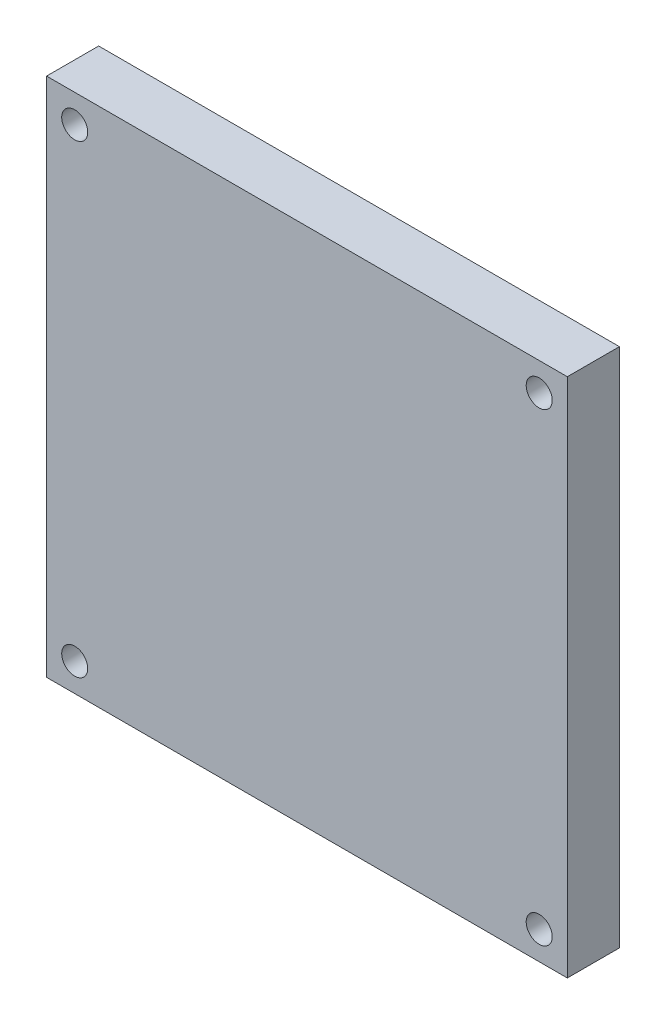
SolidWorks part; units mm, degrees
ref_plane "Front Plane" through (0, 0, 0) normal (0, 0, 1) x (1, 0, 0)
ref_plane "Top Plane" through (0, 0, 0) normal (0, 1, 0) x (1, 0, 0)
ref_plane "Right Plane" through (0, 0, 0) normal (1, 0, 0) x (0, 0, -1)
sketch "Sketch1" plane through (0, 0, 0) normal (0, 0, 1) x (1, 0, 0)
  line L0 (0, 0) -> (-50, 0)
  line L1 (-50, 0) -> (-50, 50)
  line L2 (-50, 50) -> (0, 50)
  line L3 (0, 50) -> (0, 0)
  line L4 (-50, 25) -> (0, 25) construction
  line L5 (0, 25) -> (-25, 50) construction
  line L6 (-25, 50) -> (-25, 0) construction
  line L7 (-50, 50) -> (0, 0) construction
  line L8 (-46.05, 47.3) -> (-3.95, 47.3) construction
  circle A0 centre (-47.3, 47.3) radius 1.25
  circle A1 centre (-2.7, 47.3) radius 1.25
  circle A2 centre (-47.3, 2.7) radius 1.25
  circle A3 centre (-2.7, 2.7) radius 1.25
  dimension "D3" = 2.5
  dimension "D1" = 42.1
  dimension "D2" = 50
extrude "Boss-Extrude1" add sketch "Sketch1" along normal blind 5
